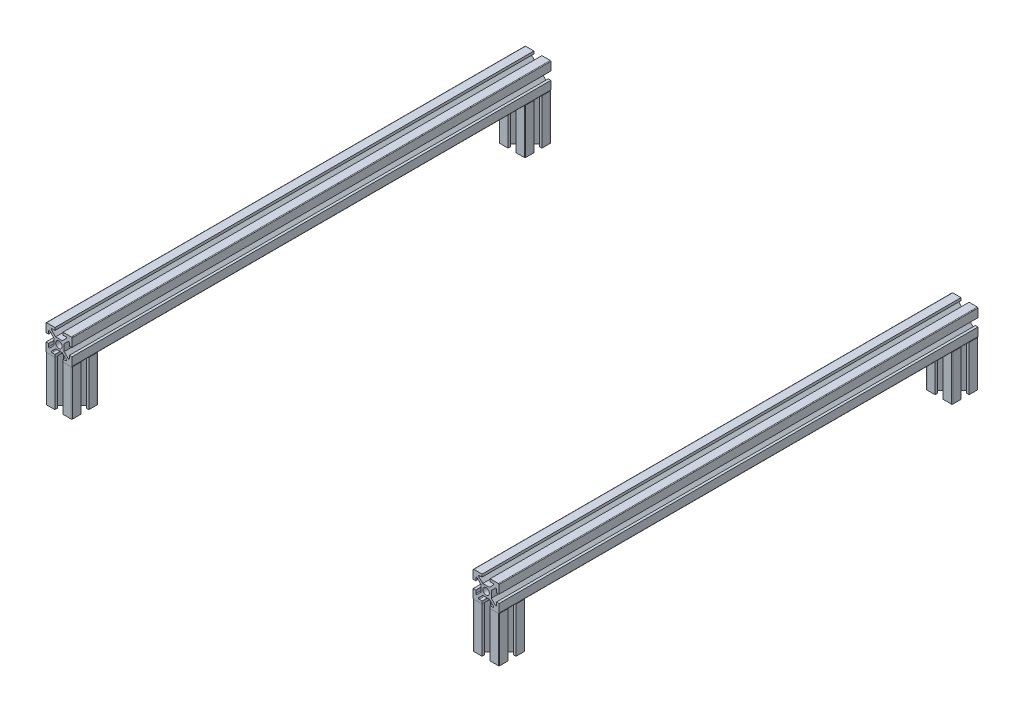
SolidWorks part; units mm, degrees
ref_plane "Front Plane" through (0, 0, 0) normal (0, 0, 1) x (1, 0, 0)
ref_plane "Top Plane" through (0, 0, 0) normal (0, 1, 0) x (1, 0, 0)
ref_plane "Right Plane" through (0, 0, 0) normal (1, 0, 0) x (0, 0, -1)
sketch3d "3DSketch1"
  line L0 (-165, 0, 175) -> (-165, -45, 175)
  line L1 (-165, 0, -175) -> (-165, 0, 175)
  line L2 (-165, 0, -175) -> (165, 0, -175) construction
  line L3 (165, 0, -175) -> (165, 0, 175)
  line L4 (-165, 0, 175) -> (165, 0, 175) construction
  line L5 (-165, 0, -175) -> (165, 0, 175) construction
  line L6 (165, 0, -175) -> (-165, 0, 175) construction
  line L7 (-165, 0, -175) -> (-165, -45, -175)
  line L8 (165, 0, 175) -> (165, -45, 175)
  line L9 (165, 0, -175) -> (165, -45, -175)
  point P0 (0, 0, 0)
  dimension "D1" = 330
  dimension "D2" = 350
  dimension "D3" = 45
other "Al extrusion 20X20(1)"
ref_plane "Plane2" through (-165, 0, -175) normal (0, 0, 1) x (1, 0, 0)
sketch "Sketch1" plane through (-165, 0, -175) normal (0, 0, 1) x (1, 0, 0)
  line L0 (0, -13.5138) -> (0, 13.5138) construction
  line L1 (-9.5, 10) -> (-3.1, 10)
  line L2 (-10, 9.5) -> (-10, 3.1)
  line L3 (-9.5, -10) -> (-3.1, -10)
  line L4 (10, 9.5) -> (10, 3.1)
  line L5 (-10, 10) -> (10, -10) construction
  line L6 (-10, -10) -> (10, 10) construction
  line L7 (-5.3787, 8) -> (-3.1, 8)
  line L8 (-8, 5.3787) -> (-8, 3.1)
  line L9 (-5.3787, -8) -> (-3.1, -8)
  line L10 (8, 5.3787) -> (8, 3.1)
  line L13 (-2.5858, 4) -> (2.5858, 4)
  line L14 (-4, 2.5858) -> (-4, -2.5858)
  line L15 (-2.5858, -4) -> (2.5858, -4)
  line L16 (4, 2.5858) -> (4, -2.5858)
  line L19 (-13.0401, 0) -> (13.0401, 0) construction
  line L20 (3.1, -10) -> (3.1, -8)
  line L21 (-10, -3.1) -> (-8, -3.1)
  line L22 (-3.1, -10) -> (-3.1, -8)
  line L23 (-10, 3.1) -> (-8, 3.1)
  line L24 (-3.1, -13.5138) -> (-3.1, 13.5138) construction
  line L25 (3.1, -13.5138) -> (3.1, 13.5138) construction
  line L26 (3.1, 10) -> (9.5, 10)
  line L27 (3.1, 8) -> (5.3787, 8)
  line L28 (3.1, -10) -> (9.5, -10)
  line L29 (3.1, -8) -> (5.3787, -8)
  line L30 (10, -3.1) -> (10, -9.5)
  line L31 (8, -3.1) -> (8, -5.3787)
  line L32 (-13.0401, -3.1) -> (13.0401, -3.1) construction
  line L33 (-13.0401, 3.1) -> (13.0401, 3.1) construction
  line L34 (-10, -3.1) -> (-10, -9.5)
  line L35 (-8, -3.1) -> (-8, -5.3787)
  line L36 (-7.1464, 5.7322) -> (-4, 2.5858)
  line L37 (-5.7322, -7.1464) -> (-2.5858, -4)
  line L38 (8, -3.1) -> (10, -3.1)
  line L39 (8, 3.1) -> (10, 3.1)
  line L40 (-3.1, 8) -> (-3.1, 10)
  line L41 (3.1, 8) -> (3.1, 10)
  line L42 (-5.7322, 7.1464) -> (-2.5858, 4)
  line L43 (-7.1464, -5.7322) -> (-4, -2.5858)
  line L44 (-10.7071, 9.2929) -> (9.2929, -10.7071) construction
  line L45 (-9.2929, 10.7071) -> (10.7071, -9.2929) construction
  line L46 (-9.2929, -10.7071) -> (10.7071, 9.2929) construction
  line L47 (-10.7071, -9.2929) -> (9.2929, 10.7071) construction
  line L52 (2.5858, 4) -> (5.7322, 7.1464)
  line L53 (4, 2.5858) -> (7.1464, 5.7322)
  line L54 (4, -2.5858) -> (7.1464, -5.7322)
  line L55 (2.5858, -4) -> (5.7322, -7.1464)
  circle A0 centre (0, 0) radius 2.5
  arc A1 (-7.1464, -5.7322) -> (-8, -5.3787) centre (-7.5, -5.3787) cw
  arc A2 (-5.7322, -7.1464) -> (-5.3787, -8) centre (-5.3787, -7.5) ccw
  arc A3 (5.7322, -7.1464) -> (5.3787, -8) centre (5.3787, -7.5) cw
  arc A4 (7.1464, -5.7322) -> (8, -5.3787) centre (7.5, -5.3787) ccw
  arc A5 (7.1464, 5.7322) -> (8, 5.3787) centre (7.5, 5.3787) cw
  arc A6 (5.7322, 7.1464) -> (5.3787, 8) centre (5.3787, 7.5) ccw
  arc A7 (-5.7322, 7.1464) -> (-5.3787, 8) centre (-5.3787, 7.5) cw
  arc A8 (-7.1464, 5.7322) -> (-8, 5.3787) centre (-7.5, 5.3787) ccw
  arc A9 (9.5, -10) -> (10, -9.5) centre (9.5, -9.5) ccw
  arc A10 (-10, -9.5) -> (-9.5, -10) centre (-9.5, -9.5) ccw
  arc A11 (-9.5, 10) -> (-10, 9.5) centre (-9.5, 9.5) ccw
  arc A12 (9.5, 10) -> (10, 9.5) centre (9.5, 9.5) cw
  point P0 (0, 0)
  point P6 (0, 0)
  point P7 (0, 0)
  point P11 (0, 0)
  point P20 (0, 0)
  point P24 (0, 0)
  dimension "D7" = 5
  dimension "D12" = 0.5
  dimension "D13" = 0.5
  dimension "D1" = 20
  dimension "D2" = 20
  dimension "D3" = 2
  dimension "D4" = 2
  dimension "D5" = 6
  dimension "D6" = 6
  dimension "D8" = 3.1
  dimension "D9" = 3.1
  dimension "D10" = 1
  dimension "D11" = 1
